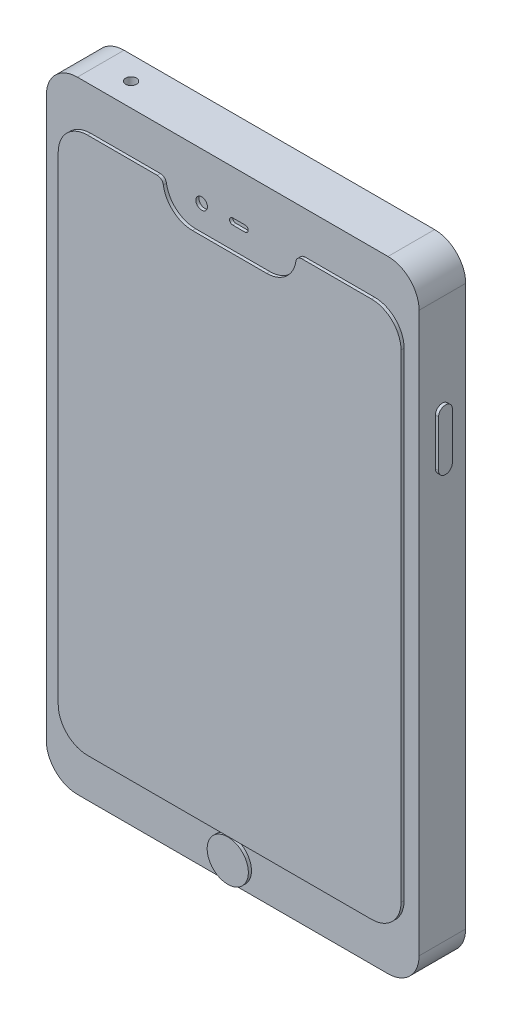
SolidWorks part; units mm, degrees
ref_plane "Front Plane" through (0, 0, 0) normal (0, 0, 1) x (1, 0, 0)
ref_plane "Top Plane" through (0, 0, 0) normal (0, 1, 0) x (1, 0, 0)
ref_plane "Right Plane" through (0, 0, 0) normal (1, 0, 0) x (0, 0, -1)
sketch "Sketch3" plane through (0, 0, 0) normal (0, 0, 1) x (1, 0, 0)
  line L1 (-50, 100) -> (50, 100)
  line L2 (-60, 90) -> (-60, -90)
  line L3 (-50, -100) -> (50, -100)
  line L4 (60, 90) -> (60, -90)
  line L5 (-60, 100) -> (60, -100) construction
  line L6 (-60, -100) -> (60, 100) construction
  arc A0 (50, -100) -> (60, -90) centre (50, -90) ccw
  arc A1 (-50, -100) -> (-60, -90) centre (-50, -90) cw
  arc A2 (60, 90) -> (50, 100) centre (50, 90) ccw
  arc A3 (-60, 90) -> (-50, 100) centre (-50, 90) cw
  point P0 (0, 0)
  dimension "D3" = 10
  dimension "D1" = 120
  dimension "D2" = 200
extrude "Boss-Extrude1" add sketch "Sketch3" along normal blind 15
sketch "Sketch4" plane through (0, 0, 0) normal (0, 0, 1) x (1, 0, 0)
  line L1 (-45.6967, 86.4798) -> (45.6967, 86.4798)
  line L2 (-55.178, 76.9985) -> (-55.178, -76.9985)
  line L3 (-45.6967, -86.4798) -> (45.6967, -86.4798)
  line L4 (55.178, 76.9985) -> (55.178, -76.9985)
  line L5 (-55.178, 86.4798) -> (55.178, -86.4798) construction
  line L6 (-55.178, -86.4798) -> (55.178, 86.4798) construction
  arc A0 (-45.6967, -86.4798) -> (-55.178, -76.9985) centre (-45.6967, -76.9985) cw
  arc A1 (45.6967, -86.4798) -> (55.178, -76.9985) centre (45.6967, -76.9985) ccw
  arc A2 (55.178, 76.9985) -> (45.6967, 86.4798) centre (45.6967, 76.9985) ccw
  arc A3 (-55.178, 76.9985) -> (-45.6967, 86.4798) centre (-45.6967, 76.9985) cw
  point P1 (0, 0)
  dimension "D1" = 9.4813
extrude "Boss-Extrude2" add sketch "Sketch4" along normal blind 16
sketch "Sketch5" plane through (0, 0, 16) normal (0, 0, 1) x (1, 0, 0)
  line L0 (45.6967, 86.4798) -> (-45.6967, 86.4798) construction
  line L1 (-0.529, 86.24) -> (0, 86.4798) construction
  line L2 (17.5037, 78.5454) -> (21.4453, 76.7587) construction
  line L3 (-11.964, 76.7587) -> (11.964, 76.7587)
  line L4 (-7.9691, 86.4798) -> (23.3096, 86.4798)
  line L5 (0, 86.4798) -> (0.529, 86.24) construction
  line L6 (-21.4453, 76.7587) -> (-17.5037, 78.5454) construction
  line L7 (-7.9691, 86.4798) -> (-23.3096, 86.4798)
  arc A0 (21.3332, 84.7864) -> (11.964, 76.7587) centre (11.964, 86.24) cw
  arc A1 (-11.964, 76.7587) -> (-21.3332, 84.7864) centre (-11.964, 86.24) cw
  arc A2 (23.3096, 86.4798) -> (21.3332, 84.7864) centre (23.3096, 84.4798) ccw
  arc A3 (-23.3096, 86.4798) -> (-21.3332, 84.7864) centre (-23.3096, 84.4798) cw
  point P0 (0, 86.4798)
  dimension "D1" = 9.4813
  dimension "D2" = 2
extrude "Cut-Extrude1" cut sketch "Sketch5" against normal blind 1
sketch "Sketch6" plane through (0, 0, 0) normal (0, 0, 1) x (1, 0, 0)
  circle A0 centre (-0.5882, -93.2398) radius 6.6264
extrude "Boss-Extrude7" add sketch "Sketch6" along normal blind 16
sketch "Sketch7" plane through (0, -100, 0) normal (0, -1, 0) x (1, 0, 0)
  line L0 (3.6848, 7.5) -> (-2.3152, 7.5) construction
  line L1 (3.6848, 6.3922) -> (-2.3152, 6.3922)
  line L2 (3.6848, 8.6078) -> (-2.3152, 8.6078)
  line L4 (-16.978, 7.5) -> (24.3476, 7.5) construction
  arc A0 (3.6848, 6.3922) -> (3.6848, 8.6078) centre (3.6848, 7.5) ccw
  arc A1 (-2.3152, 8.6078) -> (-2.3152, 6.3922) centre (-2.3152, 7.5) ccw
  point P2 (0.6848, 7.5)
  dimension "D1" = 6
extrude "Cut-Extrude3" cut sketch "Sketch7" against normal blind 10
sketch "Sketch8" plane through (0, 0, 15) normal (0, 0, 1) x (1, 0, 0)
  line L0 (0, 84.7587) -> (4, 84.7587) construction
  line L1 (0, 85.7587) -> (4, 85.7587)
  line L2 (0, 83.7587) -> (4, 83.7587)
  line L3 (-11.964, 76.7587) -> (11.964, 76.7587) construction
  arc A0 (0, 85.7587) -> (0, 83.7587) centre (0, 84.7587) ccw
  arc A1 (4, 83.7587) -> (4, 85.7587) centre (4, 84.7587) ccw
  circle A2 centre (-10, 84.7587) radius 1.861
  point P2 (2, 84.7587)
  dimension "D1" = 4
  dimension "D2" = 1
  dimension "D3" = 12
  dimension "D4" = 8
extrude "Cut-Extrude6" cut sketch "Sketch8" against normal blind 1
sketch "Sketch9" plane through (60, 0, 0) normal (1, 0, 0) x (0, 0, -1)
  line L0 (-7.5, 58.1386) -> (-7.5, 43.1386) construction
  line L1 (-5.2807, 58.1386) -> (-5.2807, 43.1386)
  line L2 (-9.7193, 58.1386) -> (-9.7193, 43.1386)
  line L3 (0, -90) -> (0, 90) construction
  arc A0 (-5.2807, 58.1386) -> (-9.7193, 58.1386) centre (-7.5, 58.1386) ccw
  arc A1 (-9.7193, 43.1386) -> (-5.2807, 43.1386) centre (-7.5, 43.1386) ccw
  point P2 (-7.5, 50.6386)
  dimension "D1" = 7.5
  dimension "D2" = 15
extrude "Boss-Extrude10" add sketch "Sketch9" along normal blind 1
sketch "Sketch10" plane through (0, -100, 0) normal (0, -1, 0) x (1, 0, 0)
  line L0 (-50, 0) -> (50, 0) construction
  circle A0 centre (-38.9267, 7.5) radius 1
  dimension "D2" = 2
  dimension "D1" = 7.5
extrude "Cut-Extrude7" cut sketch "Sketch10" against normal blind 7
sketch "Sketch11" plane through (0, 100, 0) normal (0, 1, 0) x (1, 0, 0)
  line L0 (50, 0) -> (-50, 0) construction
  circle A0 centre (-40.2237, -7.5) radius 1.75
  dimension "D2" = 3.5
  dimension "D1" = 7.5
extrude "Cut-Extrude8" cut sketch "Sketch11" against normal blind 20
sketch "Sketch12" plane through (0, 0, 0) normal (0, 0, -1) x (-1, 0, 0)
  line L7 (-18.9258, 91.9642) -> (-52.2031, 91.9642)
  line L8 (-57.2031, 86.9642) -> (-57.2031, 52.0224)
  line L9 (-18.9258, 47.0224) -> (-52.2031, 47.0224)
  line L10 (-13.9258, 86.9642) -> (-13.9258, 52.0224)
  arc A4 (-52.2031, 47.0224) -> (-57.2031, 52.0224) centre (-52.2031, 52.0224) cw
  arc A5 (-57.2031, 86.9642) -> (-52.2031, 91.9642) centre (-52.2031, 86.9642) cw
  arc A6 (-13.9258, 86.9642) -> (-18.9258, 91.9642) centre (-18.9258, 86.9642) ccw
  arc A7 (-18.9258, 47.0224) -> (-13.9258, 52.0224) centre (-18.9258, 52.0224) ccw
extrude "Boss-Extrude13" add sketch "Sketch12" along normal blind 1
sketch "Sketch13" plane through (0, 0, -1) normal (0, 0, -1) x (-1, 0, 0)
  circle A0 centre (-48.8713, 80.6491) radius 6
  circle A1 centre (-48.8713, 55.6491) radius 7.3504
  circle A2 centre (-28.6843, 66.6491) radius 5.2454
  circle A3 centre (-28.6843, 80.6491) radius 2.694
  dimension "D1" = 12
  dimension "D2" = 25
  dimension "D3" = 14
extrude "Boss-Extrude14" add sketch "Sketch13" along normal blind 1
sketch "Sketch14" plane through (0, 0, 0) normal (0, 0, -1) x (-1, 0, 0)
  arc A0 (-13.2314, 37.4316) -> (-16.5968, -36.0658) centre (0, 0) ccw
  arc A1 (-10.151, -33.979) -> (10.151, -33.979) centre (0, -44.13) cw
  arc A2 (3.6744, 33.5701) -> (-3.6744, 33.5701) centre (0, 36.9611) cw
  arc A3 (16.5968, -36.0658) -> (36.3322, -16.0051) centre (0, 0) ccw
  arc A4 (16.5968, -36.0658) -> (21.2902, -33.51) centre (0, 0) ccw
  arc A5 (-10.151, -33.979) -> (-16.5968, -36.0658) centre (-14.5066, -31.5236) cw
  arc A6 (16.5968, -36.0658) -> (10.151, -33.979) centre (14.5066, -31.5236) cw
  arc A7 (33.8962, 20.6698) -> (36.3322, -16.0051) centre (39.6468, 2.6334) ccw
  arc A8 (33.8962, 20.6698) -> (13.2314, 37.4316) centre (0, 0) ccw
  arc A9 (0, 36.9611) -> (13.2314, 59.5838) centre (17.9271, 41.6567) cw
  arc A10 (13.2314, 59.5838) -> (0, 36.9611) centre (-4.6957, 54.8881) cw
  spline S0 degree 3 poles (3.6744, 33.5701) (7.8661, 38.1123) (13.0333, 38.7088) (17.4066, 35.682) knots 0.231071 0.231071 0.231071 0.231071 1 1 1 1
  spline S1 degree 3 poles (-3.6744, 33.5701) (-7.8661, 38.1123) (-13.0333, 38.7088) (-17.4066, 35.682) knots 0.231071 0.231071 0.231071 0.231071 1 1 1 1
  dimension "D1" = 5
  dimension "D2" = 5
extrude "Boss-Extrude19" add sketch "Sketch14" along normal blind 0.2 contours A2 S1 A0 A5 A1 A6 A3 A7 A8 S0 | A10 A9
